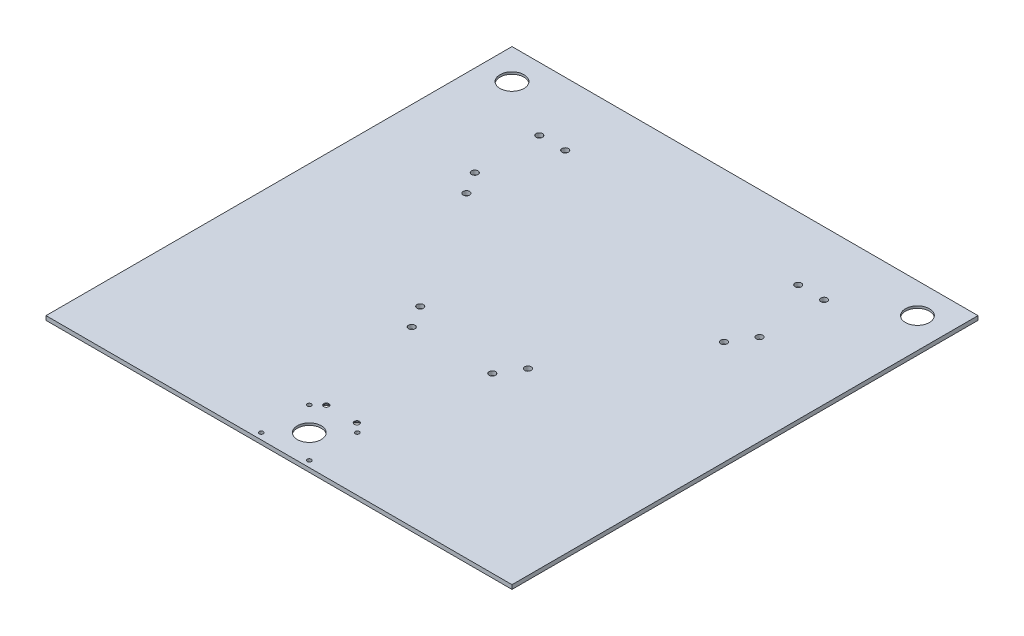
SolidWorks part; units mm, degrees
material "6061-T6 (SS)"
ref_plane "Front Plane" through (0, 0, 0) normal (0, 0, 1) x (1, 0, 0)
ref_plane "Top Plane" through (0, 0, 0) normal (0, 1, 0) x (1, 0, 0)
ref_plane "Right Plane" through (0, 0, 0) normal (1, 0, 0) x (0, 0, -1)
sketch "Sketch1" plane through (0, 0, 0) normal (0, 1, 0) x (1, 0, 0)
  line L1 (-228.6, -228.6) -> (228.6, -228.6)
  line L2 (-228.6, -228.6) -> (-228.6, 228.6)
  line L3 (-228.6, 228.6) -> (228.6, 228.6)
  line L4 (228.6, -228.6) -> (228.6, 228.6)
  line L5 (-228.6, -228.6) -> (228.6, 228.6) construction
  line L6 (-228.6, 228.6) -> (228.6, -228.6) construction
  point P0 (0, 0)
  dimension "D1" = 457.2
  dimension "D2" = 457.2
extrude "Boss-Extrude1" add sketch "Sketch1" along normal blind 4.064
sketch "Sketch2" plane through (0, 0, 0) normal (0, -1, 0) x (1, 0, 0)
  line L0 (0, -2.2352) -> (0, 2.2352) construction
  line L1 (-228.6, 228.6) -> (228.6, 228.6) construction
  line L2 (-228.6, -228.6) -> (-228.6, 228.6) construction
  line L3 (228.6, -228.6) -> (-228.6, -228.6) construction
  line L4 (228.6, 228.6) -> (228.6, -228.6) construction
  circle A0 centre (0, 198.882) radius 19.177
  circle A1 centre (-198.882, -198.882) radius 19.177
  circle A2 centre (198.882, -198.882) radius 19.177
  dimension "D1" = 38.354
  dimension "D3" = 38.354
  dimension "D4" = 38.354
  dimension "D2" = 29.718
  dimension "D5" = 29.718
  dimension "D6" = 29.718
  dimension "D7" = 29.718
  dimension "D8" = 29.718
extrude "Cut-Extrude1" cut sketch "Sketch2" against normal blind 1.905
sketch "Sketch3" plane through (0, 1.905, 0) normal (0, -1, 0) x (1, 0, 0)
  circle A0 centre (0, 198.882) radius 11.7475
  circle A1 centre (0, 198.882) radius 19.177 construction
  circle A2 centre (-198.882, -198.882) radius 11.7475
  circle A3 centre (198.882, -198.882) radius 11.7475
  circle A4 centre (198.882, -198.882) radius 19.177 construction
  circle A5 centre (-198.882, -198.882) radius 19.177 construction
  dimension "D1" = 23.495
  dimension "D2" = 23.495
  dimension "D3" = 23.495
extrude "Cut-Extrude2" cut sketch "Sketch3" against normal up to next
hole_wizard "#10-32 Tapped Hole1" positions "Sketch7" profile "Sketch8" tap size "#10-32" standard "ANSI Inch" end condition through all
sketch "Sketch7" plane through (0, 0, 0) normal (0, -1, 0) x (-1, 0, 0.0002)
  point P0 (23.6171, -222.4505)
  point P1 (-23.5293, -222.4598)
sketch "Sketch8" plane through (-23.5732, 0, 222.4552) normal (1, 0, 0) x (0, 0, -1)
  line L0 (0, 0) -> (0, 4.064)
  line L1 (0, 4.064) -> (2.0193, 4.064)
  line L2 (2.0193, 4.064) -> (2.0193, 0)
  line L3 (2.0193, 0) -> (0, 0)
  line L4 (0, -6.35) -> (0, 107.95) construction
  dimension "Thru Tap Drill Dia." = 4.0386
  dimension "Thru Tap Drill Depth" = 4.064
cosmetic thread "Hole Thread1" parameters "D1"=4.7625, "D2"=4.826
cosmetic thread "Hole Thread2" parameters "D1"=4.7625, "D2"=4.826
hole_wizard "#10-32 Tapped Hole2" positions "Sketch9" profile "Sketch10" tap size "#10-32" standard "ANSI Inch" end condition through all
sketch "Sketch9" plane through (0, 0, 0) normal (0, -1, 0) x (-1, 0, 0.0002)
  point P0 (23.6078, -175.3042)
  point P1 (-23.5386, -175.3135)
sketch "Sketch10" plane through (-23.5732, 0, 175.3088) normal (1, 0, 0) x (0, 0, -1)
  line L0 (0, 0) -> (0, 4.064)
  line L1 (0, 4.064) -> (2.0193, 4.064)
  line L2 (2.0193, 4.064) -> (2.0193, 0)
  line L3 (2.0193, 0) -> (0, 0)
  line L4 (0, -6.35) -> (0, 107.95) construction
  dimension "Thru Tap Drill Dia." = 4.0386
  dimension "Thru Tap Drill Depth" = 4.064
cosmetic thread "Hole Thread3" parameters "D1"=4.7625, "D2"=4.826
cosmetic thread "Hole Thread4" parameters "D1"=4.7625, "D2"=4.826
hole_wizard "CBORE for #10 Binding Head Machine Screw1" positions "Sketch11" profile "Sketch12" counterbore size "#10" standard "ANSI Inch" end condition through all
sketch "Sketch11" plane through (0, 0, 0) normal (0, -1, 0) x (1, 0, 0)
  point P0 (-15, 167.1745)
  point P1 (15, 167.1745)
sketch "Sketch12" plane through (-15, 0, 167.1745) normal (1, 0, 0) x (0, 0, -1)
  line L0 (0, 0) -> (0, 4.064)
  line L1 (0, 4.064) -> (2.5527, 4.064)
  line L2 (2.5527, 4.064) -> (2.5527, 3.1242)
  line L3 (2.5527, 3.1242) -> (5.5562, 3.1242)
  line L4 (5.5562, 3.1242) -> (5.5562, 0)
  line L5 (5.5562, 0) -> (0, 0)
  line L6 (0, -6.35) -> (0, 107.95) construction
  dimension "Thru Hole Dia." = 5.1054
  dimension "Thru Hole Depth" = 4.064
  dimension "C'Bore Dia." = 11.1125
  dimension "C'Bore Depth" = 3.1242
hole_wizard "1/4 (0.25) Diameter Hole1" positions "Sketch13" profile "Sketch14" hole size "1/4" standard "ANSI Inch" end condition through all
sketch "Sketch13" plane through (0, 0, 0) normal (0, -1, 0) x (-1, 0, 0)
  line L0 (0, -228.6) -> (0, 228.6) construction
  line L1 (228.6, -228.6) -> (-228.6, -228.6) construction
  line L2 (-228.6, 228.6) -> (228.6, 228.6) construction
  line L4 (-228.6, 0) -> (228.6, 0) construction
  line L5 (-228.6, -228.6) -> (-228.6, 228.6) construction
  line L6 (228.6, 228.6) -> (228.6, -228.6) construction
  line L8 (0, -122.682) -> (-178.8411, 166.4787) construction
  line L9 (-178.8411, 166.4787) -> (0, 166.4787) construction
  line L11 (0, -198.882) -> (0, -122.682) construction
  line L13 (-198.882, 198.882) -> (-178.8411, 166.4787) construction
  point P0 (-39.4955, -58.8233)
  point P2 (-52.8561, -37.2211)
  point P4 (-126.3394, 81.5909)
  point P6 (-139.7, 103.1931)
  point P8 (-139.7, 166.4787)
  point P10 (-114.3, 166.4787)
  point P56 (114.3, 166.4787)
  point P57 (139.7, 166.4787)
  point P58 (139.7, 103.1931)
  point P59 (126.3394, 81.5909)
  point P60 (52.8561, -37.2211)
  point P61 (39.4955, -58.8233)
  dimension "D1" = 25.4
  dimension "D2" = 25.4
  dimension "D3" = 25.4
  dimension "D4" = 165.1
  dimension "D5" = 88.9
  dimension "D6" = 88.9
  dimension "D7" = 76.2
  dimension "D8" = 38.1
sketch "Sketch14" plane through (39.4955, 0, 58.8233) normal (1, 0, 0) x (0, 0, -1)
  line L0 (0, 0) -> (0, 4.064)
  line L1 (0, 4.064) -> (3.175, 4.064)
  line L2 (3.175, 4.064) -> (3.175, 0)
  line L5 (3.175, 0) -> (0, 0)
  line L11 (0, -6.35) -> (0, 107.95) construction
  dimension "Thru Hole Dia." = 6.35
  dimension "Thru Hole Depth" = 4.064
